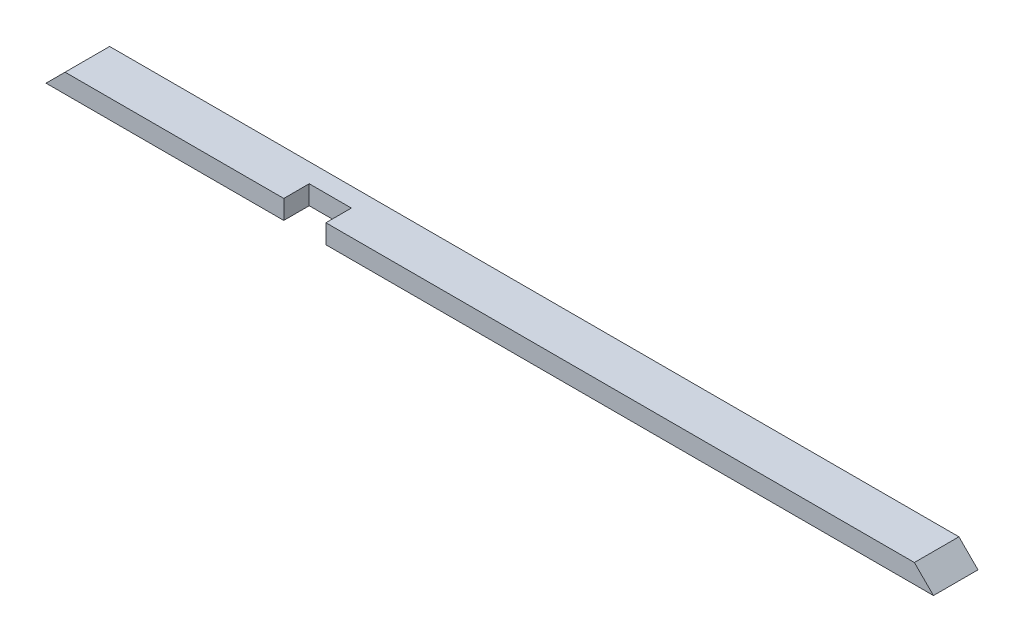
SolidWorks part; units mm, degrees
material "Pine"
ref_plane "Front Plane" through (0, 0, 0) normal (0, 0, 1) x (1, 0, 0)
ref_plane "Top Plane" through (0, 0, 0) normal (0, 1, 0) x (1, 0, 0)
ref_plane "Right Plane" through (0, 0, 0) normal (1, 0, 0) x (0, 0, -1)
sketch "Sketch1" plane through (0, 0, 0) normal (0, 1, 0) x (1, 0, 0)
  line L1 (0, 0) -> (1771.65, 0)
  line L2 (0, 0) -> (0, 88.9)
  line L3 (0, 88.9) -> (1771.65, 88.9)
  line L4 (1771.65, 0) -> (1771.65, 88.9)
  dimension "D1" = 88.9
  dimension "D2" = 1771.65
extrude "Boss-Extrude1" add sketch "Sketch1" along normal blind 38.1
sketch "Sketch2" plane through (0, 0, 0) normal (0, 0, 1) x (1, 0, 0)
  line L0 (0, 0) -> (38.1, 38.1)
  line L1 (0, 38.1) -> (1771.65, 38.1) construction
  line L2 (38.1, 38.1) -> (0, 38.1)
  line L3 (0, 38.1) -> (0, 0)
  line L5 (1771.65, 0) -> (1771.65, 38.1)
  line L9 (1771.65, 38.1) -> (1733.55, 38.1)
  line L10 (1733.55, 38.1) -> (1771.65, 0)
  dimension "D1" = 38.1
  dimension "D2" = 38.1
  dimension "D3" = 38.1
extrude "Cut-Extrude1" cut sketch "Sketch2" against normal through all
sketch "Sketch3" plane through (0, 0, 0) normal (0, -1, 0) x (1, 0, 0)
  line L0 (0, 0) -> (1771.65, 0) construction
  line L1 (558.8, 0) -> (474.6625, 0)
  line L2 (558.8, 0) -> (558.8, -50.8)
  line L3 (558.8, -50.8) -> (474.6625, -50.8)
  line L4 (474.6625, 0) -> (474.6625, -50.8)
  line L5 (0, -88.9) -> (0, 0) construction
  point P8 (474.6625, -25.4)
  dimension "D1" = 84.1375
  dimension "D2" = 50.8
  dimension "D3" = 474.6625
extrude "Cut-Extrude2" cut sketch "Sketch3" against normal through all
